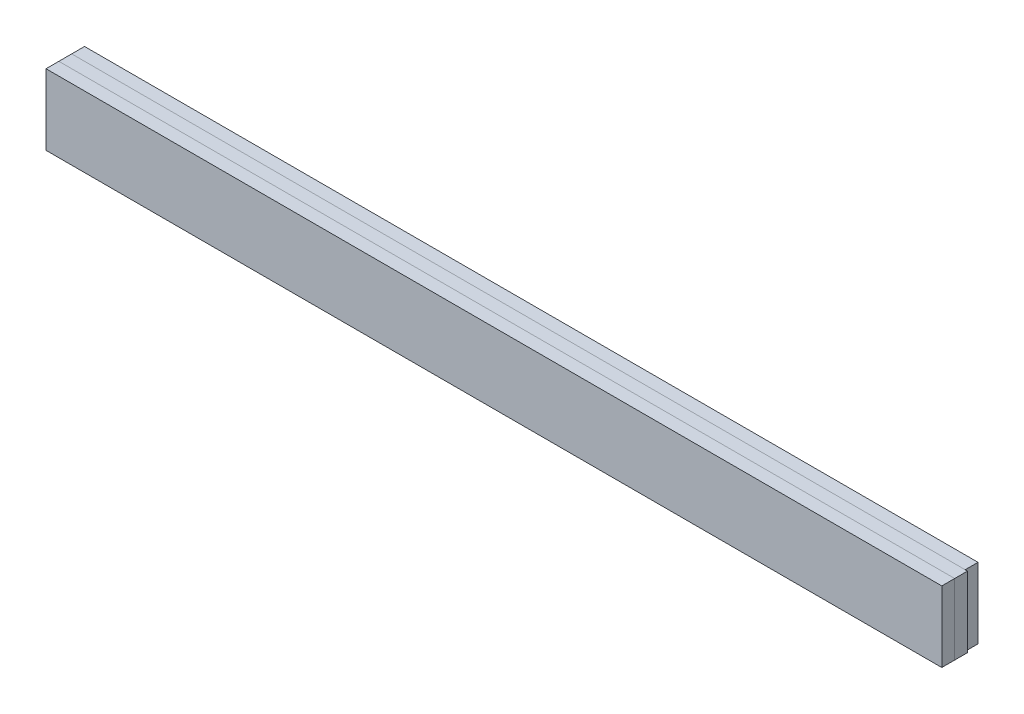
SolidWorks part; units mm, degrees
material "Rubber"
ref_plane "Front Plane" through (0, 0, 0) normal (0, 0, 1) x (1, 0, 0)
ref_plane "Top Plane" through (0, 0, 0) normal (0, 1, 0) x (1, 0, 0)
ref_plane "Right Plane" through (0, 0, 0) normal (1, 0, 0) x (0, 0, -1)
sketch "Sketch1" plane through (0, 0, 0) normal (0, 0, 1) x (1, 0, 0)
  line L0 (55, 0) -> (-55, 0) construction
  line L1 (-34.85, 5.5) -> (34.85, 5.5)
  line L2 (-34.85, 5.5) -> (-34.85, 0)
  line L3 (-34.85, 0) -> (34.85, 0)
  line L4 (34.85, 5.5) -> (34.85, 0)
  dimension "D1" = 69.7
  dimension "D2" = 5.5
extrude "Boss-Extrude1" add sketch "Sketch1" along normal mid plane 1
sketch "Sketch2" plane through (0, 0, 0.5) normal (0, 0, 1) x (1, 0, 0)
  line L0 (34.85, 0) -> (34.85, 5.5) construction
  line L1 (-34.85, 5.5) -> (34.85, 5.5)
  line L2 (-34.85, 5.5) -> (-34.85, 0)
  line L3 (-34.85, 0) -> (34.85, 0)
  line L4 (34.85, 5.5) -> (34.85, 0)
extrude "Boss-Extrude2" add sketch "Sketch2" along normal blind 1 separate body
sketch "Sketch3" plane through (0, 0, -0.5) normal (0, 0, -1) x (-1, 0, 0)
  line L0 (-34.85, 5.5) -> (34.85, 5.5) construction
  line L1 (-34.6675, 5.5) -> (34.85, 5.5)
  line L2 (-34.6675, 5.5) -> (-34.6675, 0)
  line L3 (-34.6675, 0) -> (34.85, 0)
  line L4 (34.85, 5.5) -> (34.85, 0)
extrude "Boss-Extrude3" add sketch "Sketch3" along normal blind 1 separate body
